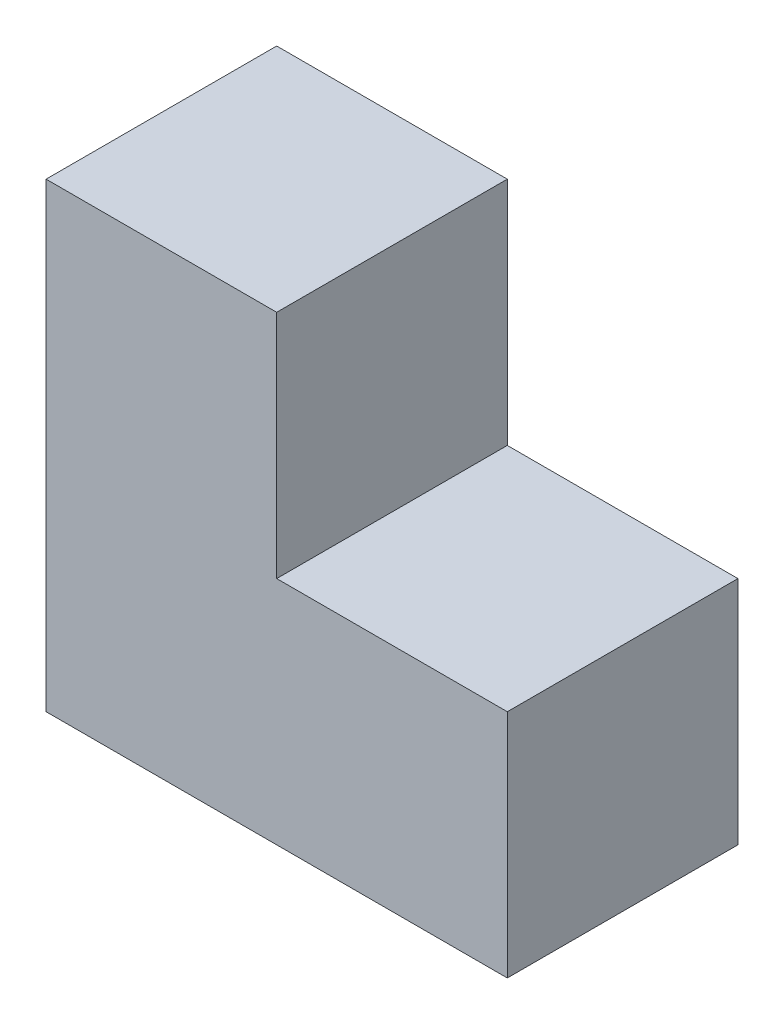
SolidWorks part; units mm, degrees
ref_plane "Front Plane" through (0, 0, 0) normal (0, 0, 1) x (1, 0, 0)
ref_plane "Top Plane" through (0, 0, 0) normal (0, 1, 0) x (1, 0, 0)
ref_plane "Right Plane" through (0, 0, 0) normal (1, 0, 0) x (0, 0, -1)
sketch "Sketch1" plane through (0, 0, 0) normal (0, 0, 1) x (1, 0, 0)
  line L0 (-56.5011, 0) -> (70.2376, 0) construction
  line L1 (0, 40.3672) -> (0, -32.9806) construction
  line L2 (-30, 60) -> (-30, 0)
  line L3 (-30, 0) -> (30, 0)
  line L4 (30, 0) -> (30, 30)
  line L5 (30, 30) -> (0, 30)
  line L6 (0, 30) -> (0, 60)
  line L7 (0, 60) -> (-30, 60)
  point P7 (0, 0)
  point P13 (-36.2851, 34.5356)
  dimension "D1" = 60
  dimension "D2" = 30
  dimension "D3" = 30
  dimension "D4" = 60
extrude "Boss-Extrude1" add sketch "Sketch1" against normal blind 30
